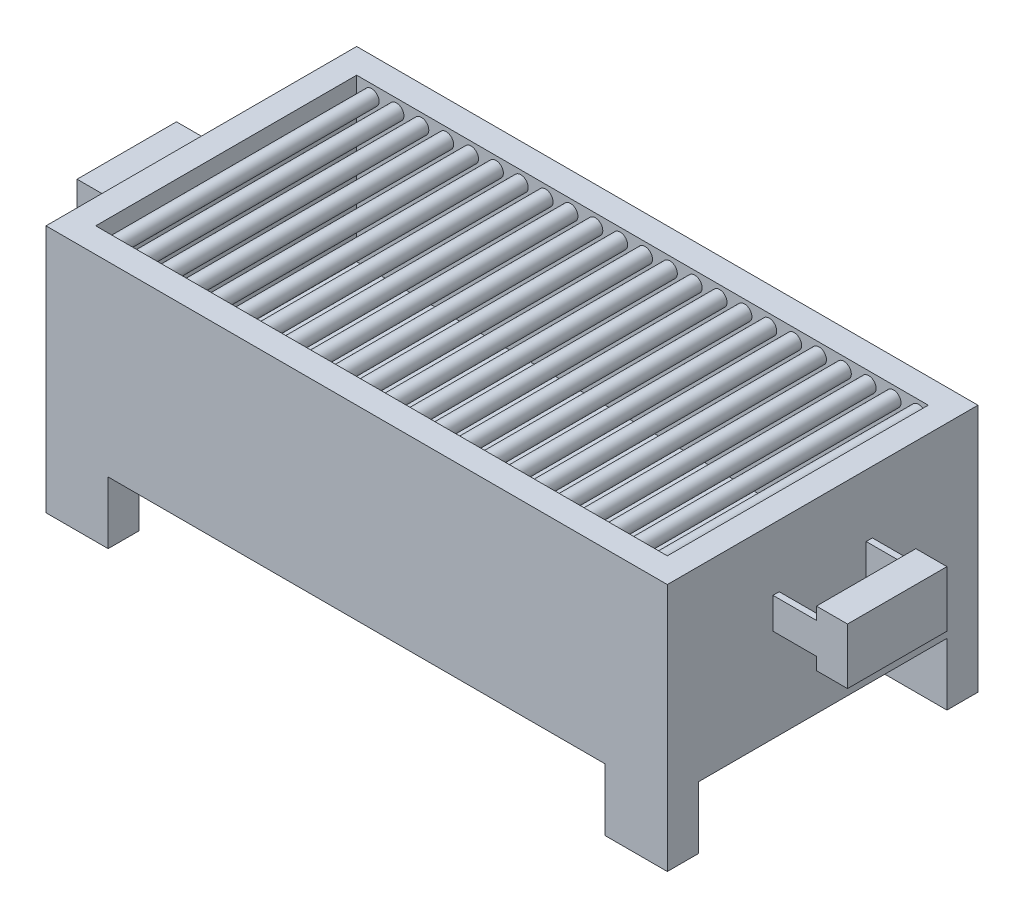
SolidWorks part; units mm, degrees
ref_plane "Front Plane" through (0, 0, 0) normal (0, 0, 1) x (1, 0, 0)
ref_plane "Top Plane" through (0, 0, 0) normal (0, 1, 0) x (1, 0, 0)
ref_plane "Right Plane" through (0, 0, 0) normal (1, 0, 0) x (0, 0, -1)
sketch "Sketch1" plane through (0, 0, 0) normal (0, 0, 1) x (1, 0, 0)
  line L1 (-25, 20) -> (25, 20)
  line L2 (-25, 20) -> (-25, 0)
  line L3 (-25, 0) -> (25, 0)
  line L4 (25, 20) -> (25, 0)
  point P4 (0, 0)
  dimension "D1" = 50
  dimension "D2" = 20
extrude "Boss-Extrude1" add sketch "Sketch1" along normal mid plane 25
sketch "Sketch2" plane through (0, 0, 0) normal (0, 1, 0) x (1, 0, 0)
  line L1 (23, -10.5) -> (-23, -10.5)
  line L2 (23, -10.5) -> (23, 10.5)
  line L3 (23, 10.5) -> (-23, 10.5)
  line L4 (-23, -10.5) -> (-23, 10.5)
  line L5 (23, -10.5) -> (-23, 10.5) construction
  line L6 (23, 10.5) -> (-23, -10.5) construction
  point P0 (0, 0)
  dimension "D1" = 46
  dimension "D2" = 21
extrude "Cut-Extrude1" cut sketch "Sketch2" against normal blind 13 from surface at 20 starting at face at (0, 20, 0)
sketch "Sketch3" plane through (0, 0, 0) normal (0, 0, 1) x (1, 0, 0)
  circle A0 centre (-21.795, 19.0651) radius 0.6
  circle A1 centre (-19.795, 19.0651) radius 0.6
  circle A2 centre (-17.795, 19.0651) radius 0.6
  circle A3 centre (-15.795, 19.0651) radius 0.6
  circle A4 centre (-13.795, 19.0651) radius 0.6
  circle A5 centre (-11.795, 19.0651) radius 0.6
  circle A6 centre (-9.795, 19.0651) radius 0.6
  circle A7 centre (-7.795, 19.0651) radius 0.6
  circle A8 centre (-5.795, 19.0651) radius 0.6
  circle A9 centre (-3.795, 19.0651) radius 0.6
  circle A10 centre (-1.795, 19.0651) radius 0.6
  circle A11 centre (0.205, 19.0651) radius 0.6
  circle A12 centre (2.205, 19.0651) radius 0.6
  circle A13 centre (4.205, 19.0651) radius 0.6
  circle A14 centre (6.205, 19.0651) radius 0.6
  circle A15 centre (8.205, 19.0651) radius 0.6
  circle A16 centre (10.205, 19.0651) radius 0.6
  circle A17 centre (12.205, 19.0651) radius 0.6
  circle A18 centre (14.205, 19.0651) radius 0.6
  circle A19 centre (16.205, 19.0651) radius 0.6
  circle A20 centre (18.205, 19.0651) radius 0.6
  circle A21 centre (20.205, 19.0651) radius 0.6
  circle A22 centre (22.205, 19.0651) radius 0.6
  dimension "D1" = 1.2
  dimension "D2" = 23
extrude "Boss-Extrude2" add sketch "Sketch3" along normal blind 21 from surface at -10.5 starting at face at (0, 13.5, -10.5)
sketch "Sketch4" plane through (0, 0, 0) normal (1, 0, 0) x (0, 0, -1)
  line L0 (10, 0) -> (10, 5)
  line L1 (-12.5, 0) -> (12.5, 0) construction
  line L2 (10, 5) -> (-10, 5)
  line L3 (-10, 5) -> (-10, 0)
  line L4 (-10, 0) -> (10, 0)
  point P6 (0, 5)
  dimension "D1" = 5
  dimension "D2" = 20
extrude "Cut-Extrude2" cut sketch "Sketch4" against normal mid plane 60
sketch "Sketch5" plane through (0, 0, 0) normal (0, 0, 1) x (1, 0, 0)
  line L0 (-20, 0) -> (20, 0)
  line L2 (-25, 0) -> (25, 0) construction
  line L3 (-20, 0) -> (-20, 5)
  line L4 (-20, 5) -> (20, 5)
  line L5 (20, 5) -> (20, 0)
  point P4 (0, 5)
  dimension "D1" = 5
  dimension "D2" = 40
extrude "Cut-Extrude3" cut sketch "Sketch5" along normal mid plane 40
sketch "Sketch6" plane through (0, 0, 0) normal (0, 0, 1) x (1, 0, 0)
  line L0 (-25, 15) -> (-28.5, 15)
  line L1 (-25, 20) -> (-25, 0) construction
  line L2 (-25, 12.5) -> (-28.5, 12.5)
  line L3 (-28.5, 15) -> (-28.5, 16)
  line L4 (-28.5, 16) -> (-31, 16)
  line L5 (-31, 16) -> (-31, 11.5)
  line L6 (-31, 11.5) -> (-28.5, 11.5)
  line L7 (-28.5, 11.5) -> (-28.5, 12.5)
  line L8 (25, 20) -> (-25, 20) construction
  line L9 (25, 15) -> (28.5, 15)
  line L10 (25, 0) -> (25, 20) construction
  line L11 (28.5, 15) -> (28.5, 16)
  line L12 (28.5, 16) -> (31, 16)
  line L13 (31, 16) -> (31, 11.5)
  line L14 (31, 11.5) -> (28.5, 11.5)
  line L15 (28.5, 11.5) -> (28.5, 12.5)
  line L16 (28.5, 12.5) -> (25, 12.5)
  line L17 (-25, 15) -> (-25, 12.5)
  line L18 (25, 15) -> (25, 12.5)
  point P22 (26.75, 15)
  dimension "D1" = 5
  dimension "D2" = 2.5
  dimension "D3" = 4.5
  dimension "D4" = 1
  dimension "D5" = 1
  dimension "D6" = 2.5
  dimension "D7" = 3.5
  dimension "D8" = 2.5
  dimension "D9" = 4.5
  dimension "D10" = 1
  dimension "D11" = 3.5
  dimension "D12" = 2.5
extrude "Boss-Extrude3" add sketch "Sketch6" along normal mid plane 8
sketch "Sketch7" plane through (0, 0, 0) normal (0, 1, 0) x (1, 0, 0)
  line L0 (-25, -4) -> (-25, 4) construction
  line L1 (-28, 3.5) -> (-25, 3.5)
  line L2 (-28, 3.5) -> (-28, -3.5)
  line L3 (-28, -3.5) -> (-25, -3.5)
  line L4 (-25, 3.5) -> (-25, -3.5)
  line L5 (25, -4) -> (25, 4) construction
  line L6 (25, 3.5) -> (28, 3.5)
  line L7 (25, 3.5) -> (25, -3.5)
  line L8 (25, -3.5) -> (28, -3.5)
  line L9 (28, 3.5) -> (28, -3.5)
  line L10 (-25, -4) -> (-28.5, -4) construction
  line L11 (-28.5, -4) -> (-28.5, 4) construction
  line L12 (28.5, 4) -> (25, 4) construction
  line L13 (28.5, -4) -> (28.5, 4) construction
  point P12 (0, 0)
  point P13 (0, 0)
  point P14 (-26.5, -3.5)
  dimension "D1" = 0.5
  dimension "D2" = 0.5
  dimension "D3" = 0.5
  dimension "D4" = 0.5
extrude "Cut-Extrude4" cut sketch "Sketch7" against normal blind 8 from surface at 15 starting at face at (-26.75, 15, 0)
